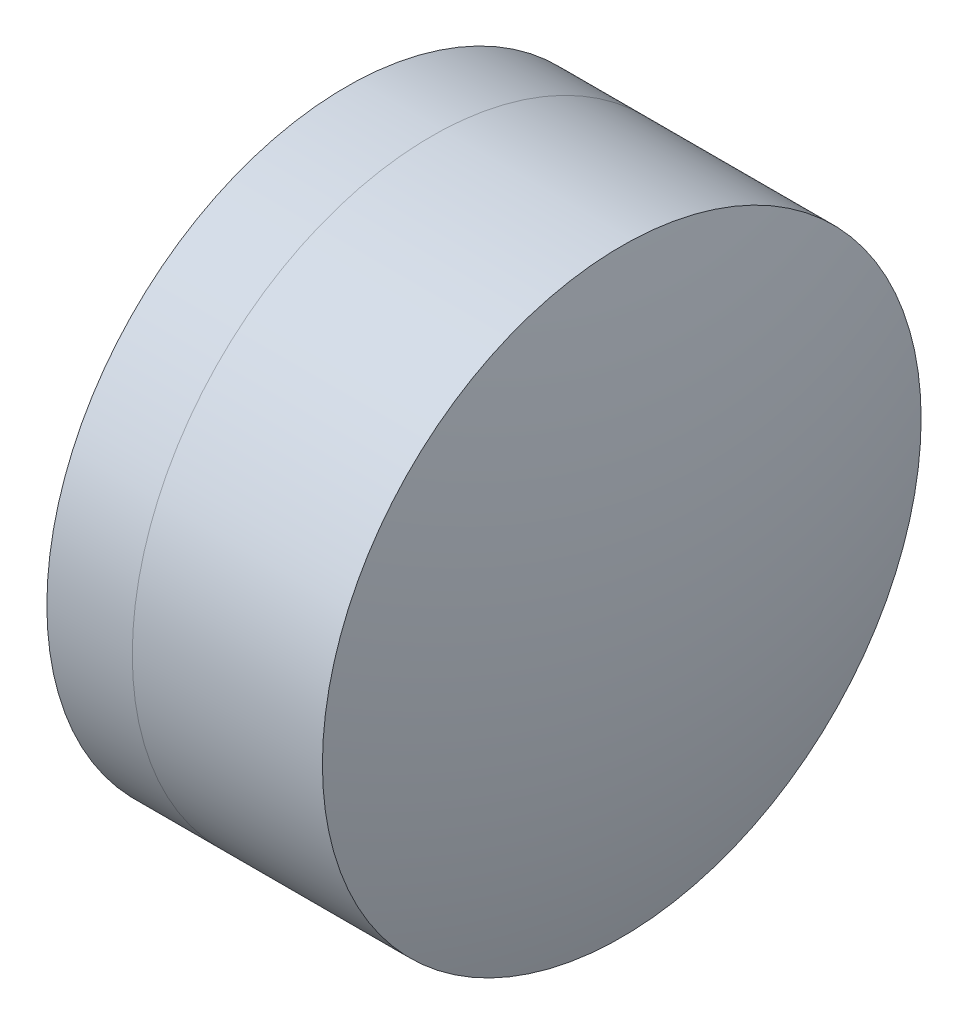
SolidWorks part; units mm, degrees
ref_plane "前视基准面" through (0, 0, 0) normal (0, 0, 1) x (1, 0, 0)
ref_plane "上视基准面" through (0, 0, 0) normal (0, 1, 0) x (1, 0, 0)
ref_plane "右视基准面" through (0, 0, 0) normal (1, 0, 0) x (0, 0, -1)
sketch "草图1" plane through (0, 0, 0) normal (0, 1, 0) x (1, 0, 0)
  line L0 (-0.8161, 0) -> (5.81, 0) construction
  line L1 (1.4711, -3.175) -> (2.377, -3.175)
  line L2 (1.4711, 3.175) -> (2.377, 3.175)
  arc A0 (2.377, -3.175) -> (2.377, 3.175) centre (-1.342, 0) ccw
  arc A1 (1.4711, 3.175) -> (1.4711, -3.175) centre (23.948, 0) ccw
  point P10 (1.248, 0)
  point P11 (3.548, 0)
  dimension "D3" = 22.7
  dimension "D4" = 4.89
  dimension "D1" = 3.175
  dimension "D2" = 3.175
  dimension "D5" = 2.3
revolve "旋转1" add sketch "草图1" angle 360 about L0
sketch "草图2" plane through (0, 0, 0) normal (0, 1, 0) x (1, 0, 0)
  line L0 (-0.5519, 0) -> (5.6049, 0) construction
  line L2 (2.377, 3.175) -> (4.3936, 3.175)
  line L3 (2.377, -3.175) -> (4.3936, -3.175)
  arc A0 (4.3936, -3.175) -> (4.3936, 3.175) centre (-6.472, 0) ccw
  arc A1 (2.377, -3.175) -> (2.377, 3.175) centre (-1.342, 0) ccw construction
  arc A2 (2.377, -3.175) -> (2.377, 3.175) centre (-1.342, 0) ccw
  point P4 (3.548, 0)
  point P12 (4.848, 0)
  dimension "D1" = 11.32
  dimension "D2" = 1.3
revolve "旋转2" add sketch "草图2" angle 360 about L0
